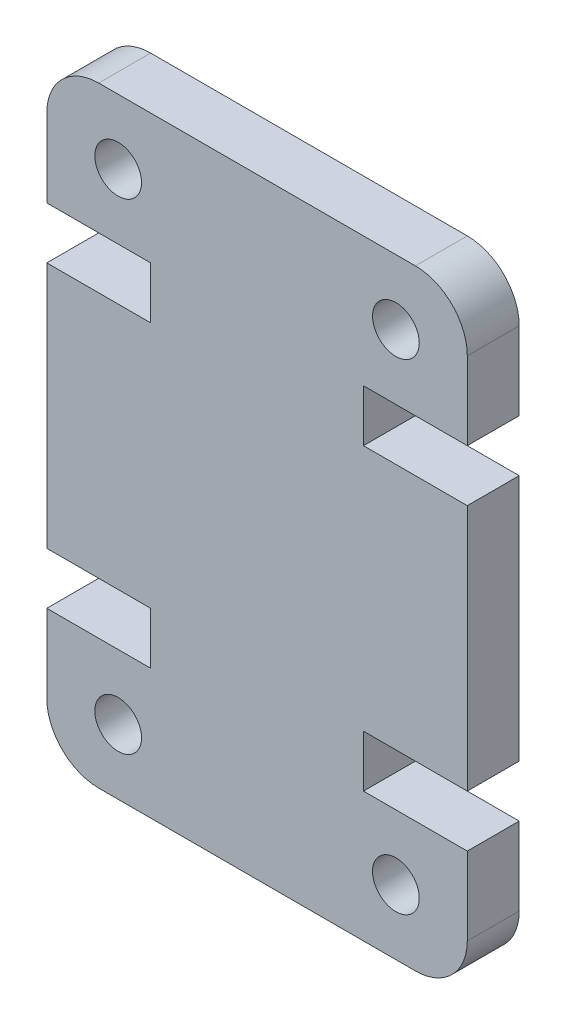
SolidWorks part; units mm, degrees
ref_plane "Front Plane" through (0, 0, 0) normal (0, 0, 1) x (1, 0, 0)
ref_plane "Top Plane" through (0, 0, 0) normal (0, 1, 0) x (1, 0, 0)
ref_plane "Right Plane" through (0, 0, 0) normal (1, 0, 0) x (0, 0, -1)
sketch "Sketch1" plane through (0, 0, 0) normal (0, 0, 1) x (1, 0, 0)
  line L0 (8.1, 23.525) -> (8.1, 0) construction
  line L1 (0, 11.7625) -> (16.2, 11.7625) construction
  line L2 (16.2, 5) -> (16.2, 2)
  line L3 (12.2, 5) -> (16.2, 5)
  line L4 (16.2, 7) -> (12.2, 7)
  line L5 (12.2, 7) -> (12.2, 5)
  line L6 (16.2, 7) -> (16.2, 16.525)
  line L7 (0, 18.525) -> (0, 21.525)
  line L8 (4, 18.525) -> (0, 18.525)
  line L9 (0, 16.525) -> (4, 16.525)
  line L10 (4, 16.525) -> (4, 18.525)
  line L11 (2, 23.525) -> (14.2, 23.525)
  line L12 (12.2, 16.525) -> (12.2, 18.525)
  line L13 (16.2, 16.525) -> (12.2, 16.525)
  line L14 (12.2, 18.525) -> (16.2, 18.525)
  line L15 (16.2, 18.525) -> (16.2, 21.525)
  line L20 (0, 7) -> (0, 16.525)
  line L23 (2, 0) -> (14.2, 0)
  line L30 (4, 7) -> (4, 5)
  line L32 (0, 7) -> (4, 7)
  line L33 (4, 5) -> (0, 5)
  line L39 (0, 5) -> (0, 2)
  circle A0 centre (13.45, 2.5) radius 0.9
  arc A2 (16.2, 2) -> (14.2, 0) centre (14.2, 2) cw
  circle A4 centre (2.75, 21.025) radius 0.9
  arc A5 (0, 21.525) -> (2, 23.525) centre (2, 21.525) cw
  arc A7 (16.2, 21.525) -> (14.2, 23.525) centre (14.2, 21.525) ccw
  circle A9 centre (13.45, 21.025) radius 0.9
  arc A11 (0, 2) -> (2, 0) centre (2, 2) ccw
  circle A13 centre (2.75, 2.5) radius 0.9
  point P18 (8.1, 11.7625)
  dimension "D2" = 2
  dimension "D4" = 1.8
  dimension "D3" = 2.75
  dimension "D5" = 8.1
  dimension "D6" = 2.5
  dimension "D7" = 5
  dimension "D10" = 11.7625
extrude "Boss-Extrude1" add sketch "Sketch1" along normal blind 2
equation "\"D10@Sketch1\"= ( \"HL@parametersSketch@prostheticParameters.SLDPRT\" * 0.165 - 3 - 4 ) / 2 'MIP length - Sil. Sht MIP - Sil. Sht DIP"
equation "\"D5@Sketch1\"= \"fingerWidth@parametersSketch@prostheticParameters.SLDPRT\" / 2'MIP width"
equation "\"D4@Sketch1\"= 1.5 + \"tol1@parametersSketch@prostheticParameters.SLDPRT\""
